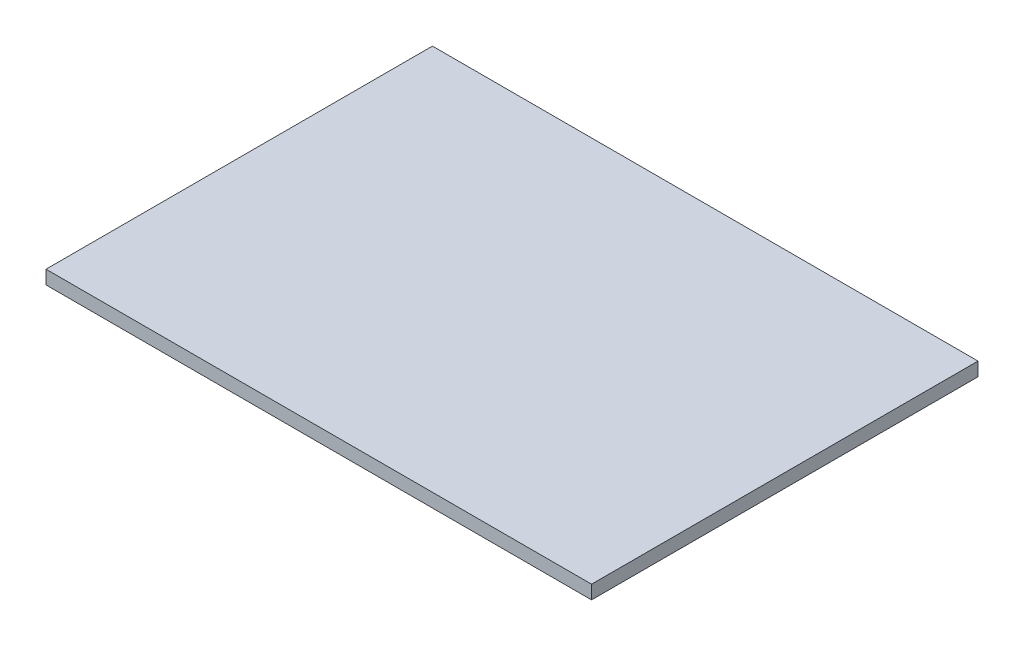
SolidWorks part; units mm, degrees
ref_plane "Спереди" through (0, 0, 0) normal (0, 0, 1) x (1, 0, 0)
ref_plane "Сверху" through (0, 0, 0) normal (0, 1, 0) x (1, 0, 0)
ref_plane "Справа" through (0, 0, 0) normal (1, 0, 0) x (0, 0, -1)
sketch "Эскиз1" plane through (0, 0, 0) normal (0, 1, 0) x (1, 0, 0)
  line L1 (-60, 42.5) -> (60, 42.5)
  line L2 (-60, 42.5) -> (-60, -42.5)
  line L3 (-60, -42.5) -> (60, -42.5)
  line L4 (60, 42.5) -> (60, -42.5)
  line L5 (-60, 42.5) -> (60, -42.5) construction
  line L6 (-60, -42.5) -> (60, 42.5) construction
  point P0 (0, 0)
extrude "Бобышка-Вытянуть1" add sketch "Эскиз1" along normal blind 3
